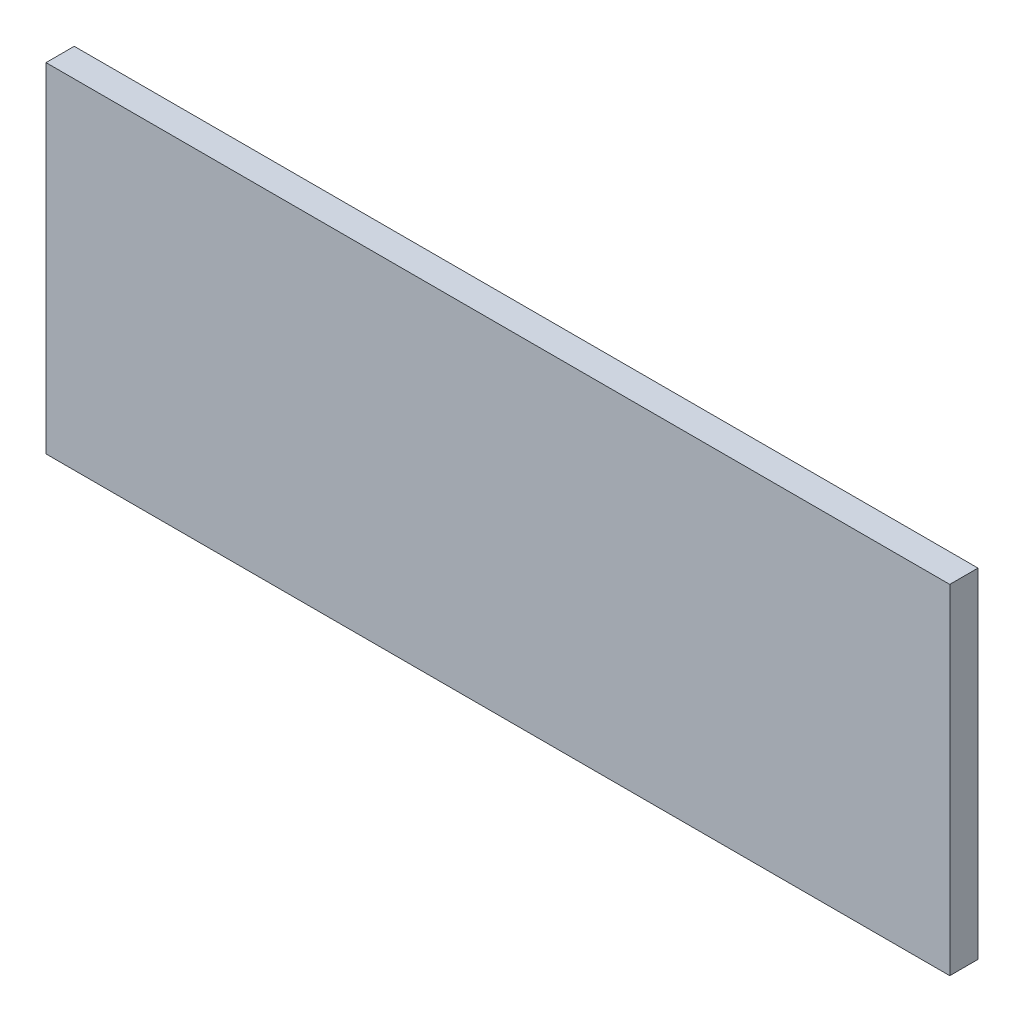
SolidWorks part; units mm, degrees
ref_plane "Front Plane" through (0, 0, 0) normal (0, 0, 1) x (1, 0, 0)
ref_plane "Top Plane" through (0, 0, 0) normal (0, 1, 0) x (1, 0, 0)
ref_plane "Right Plane" through (0, 0, 0) normal (1, 0, 0) x (0, 0, -1)
sketch "Sketch1" plane through (0, 0, 0) normal (0, 0, 1) x (1, 0, 0)
  line L1 (0, 0) -> (609.6, 0)
  line L2 (0, 0) -> (0, -228.6)
  line L3 (0, -228.6) -> (609.6, -228.6)
  line L4 (609.6, 0) -> (609.6, -228.6)
  dimension "D1" = 609.6
  dimension "D2" = 228.6
extrude "Boss-Extrude1" add sketch "Sketch1" along normal blind 19.05
